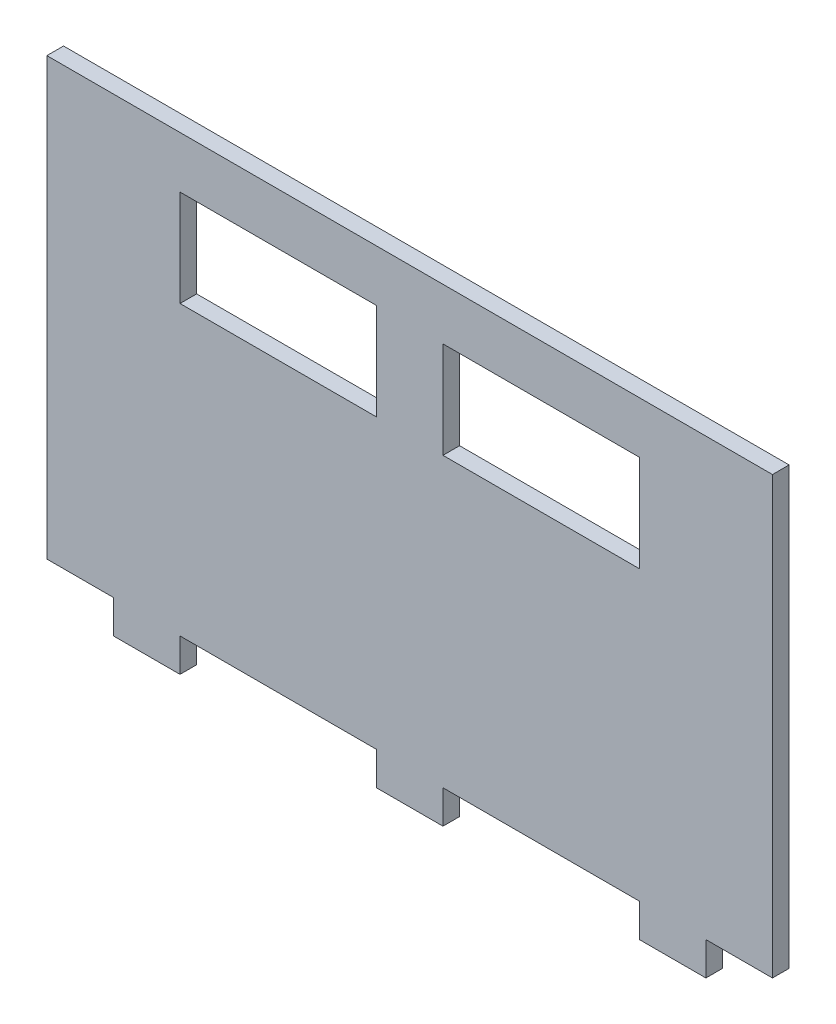
SolidWorks part; units mm, degrees
ref_plane "Front Plane" through (0, 0, 0) normal (0, 0, 1) x (1, 0, 0)
ref_plane "Top Plane" through (0, 0, 0) normal (0, 1, 0) x (1, 0, 0)
ref_plane "Right Plane" through (0, 0, 0) normal (1, 0, 0) x (0, 0, -1)
sketch "Sketch1" plane through (0, 0, 0) normal (0, 0, 1) x (1, 0, 0)
  line L0 (-97.461, -57.5) -> (88.9792, -57.5) construction
  line L1 (-109, 65.5) -> (109, 65.5)
  line L2 (-109, 65.5) -> (-109, -65.5)
  line L3 (-109, -65.5) -> (109, -65.5)
  line L4 (109, 65.5) -> (109, -65.5)
  line L5 (-109, 65.5) -> (109, -65.5) construction
  line L6 (-109, -65.5) -> (109, 65.5) construction
  line L7 (-97.461, -52.5) -> (88.9792, -52.5) construction
  line L9 (-89, -65.5) -> (-69, -65.5)
  line L10 (-89, -65.5) -> (-89, -75.5)
  line L11 (-89, -75.5) -> (-69, -75.5)
  line L12 (-69, -65.5) -> (-69, -75.5)
  line L13 (-10, -65.5) -> (10, -65.5)
  line L14 (-10, -65.5) -> (-10, -75.5)
  line L15 (-10, -75.5) -> (10, -75.5)
  line L16 (10, -65.5) -> (10, -75.5)
  line L17 (69, -65.5) -> (89, -65.5)
  line L18 (69, -65.5) -> (69, -75.5)
  line L19 (69, -75.5) -> (89, -75.5)
  line L20 (89, -65.5) -> (89, -75.5)
  line L21 (10, 50) -> (69, 50)
  line L22 (10, 50) -> (10, 21)
  line L23 (10, 21) -> (69, 21)
  line L24 (69, 50) -> (69, 21)
  line L25 (-69, 21) -> (-10, 21)
  line L26 (-69, 21) -> (-69, 50)
  line L27 (-69, 50) -> (-10, 50)
  line L28 (-10, 21) -> (-10, 50)
  point P0 (0, 0)
  point P22 (-69, -70.5)
  dimension "D1" = 131
  dimension "D2" = 218
  dimension "D3" = 8
  dimension "D4" = 5
  dimension "D5" = 10
  dimension "D6" = 20
  dimension "D7" = 20
  dimension "D8" = 59
  dimension "D9" = 10
  dimension "D10" = 20
  dimension "D11" = 59
  dimension "D12" = 10
  dimension "D13" = 20
  dimension "D14" = 59
  dimension "D15" = 59
  dimension "D16" = 29
  dimension "D17" = 29
  dimension "D18" = 102.5
  dimension "D19" = 102.5
  dimension "D20" = 20
extrude "Boss-Extrude1" add sketch "Sketch1" along normal blind 5 contours L4 L1 L2 L3 L28 L25 L26 L27 L21 L24 L23 L22 | L20 L3 L18 L19 | L16 L3 L14 L15 | L12 L3 L10 L11
